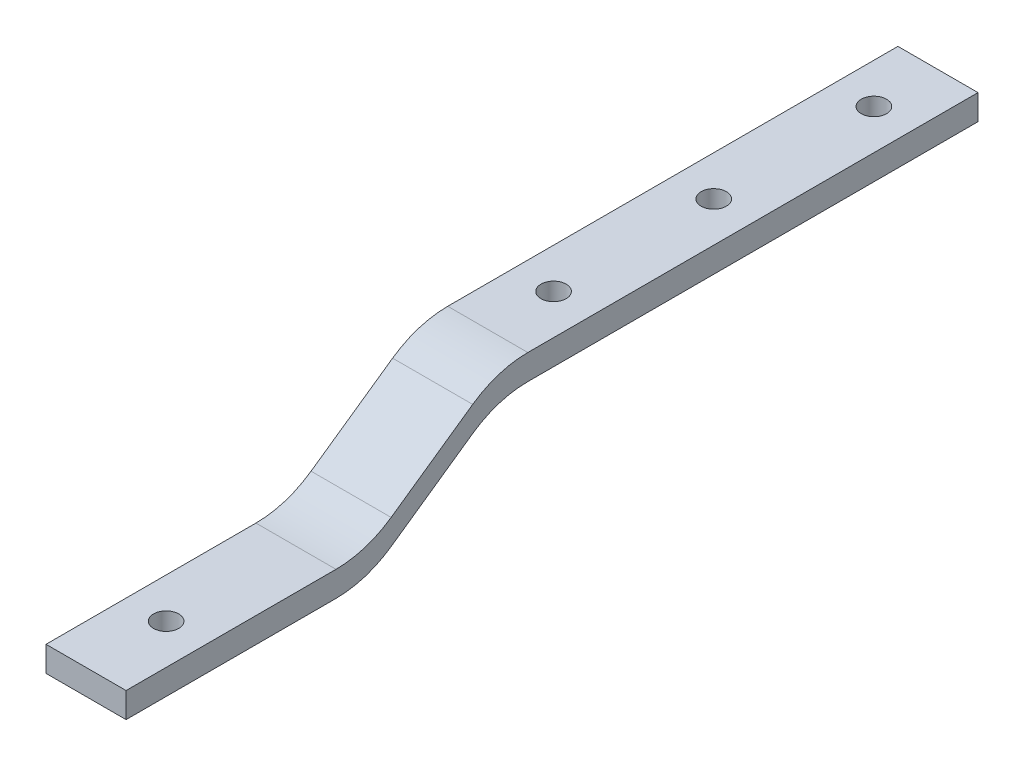
SolidWorks part; units mm, degrees
ref_plane "Front Plane" through (0, 0, 0) normal (0, 0, 1) x (1, 0, 0)
ref_plane "Top Plane" through (0, 0, 0) normal (0, 1, 0) x (1, 0, 0)
ref_plane "Right Plane" through (0, 0, 0) normal (1, 0, 0) x (0, 0, -1)
sketch "Sketch1" plane through (0, 0, 0) normal (1, 0, 0) x (0, 0, -1)
  line L0 (0, 2) -> (19.05, 2)
  line L1 (19.05, 2) -> (29.4532, 9.2844)
  line L2 (67.5532, 9.2844) -> (29.4532, 9.2844)
  line L3 (67.5532, 7.2844) -> (67.5532, 9.2844)
  line L4 (67.5532, 7.2844) -> (29.4532, 7.2844)
  line L5 (29.4532, 7.2844) -> (19.05, 0)
  line L6 (19.05, 0) -> (0, 0)
  line L7 (0, 0) -> (0, 2)
  dimension "D1" = 2
  dimension "D2" = 2
  dimension "D3" = 19.05
  dimension "D4" = 38.1
  dimension "D5" = 145
  dimension "D6" = 12.7
extrude "Boss-Extrude1" add sketch "Sketch1" along normal blind 6.35
sketch "Sketch2" plane through (0, 2, 0) normal (0, 1, 0) x (1, 0, 0)
  line L0 (6.35, 19.05) -> (6.35, 0) construction
  line L1 (6.35, 0) -> (0, 0) construction
  circle A0 centre (3.175, 6.35) radius 1
  dimension "D1" = 2
  dimension "D2" = 3.175
  dimension "D3" = 6.35
extrude "Cut-Extrude1" cut sketch "Sketch2" against normal up to surface (2 mm away) up to face at (3.175, 0, -9.525)
sketch "Sketch3" plane through (0, 9.2844, 0) normal (0, 1, 0) x (1, 0, 0)
  line L0 (6.35, 67.5532) -> (0, 67.5532) construction
  line L1 (6.35, 67.5532) -> (6.35, 29.4532) construction
  circle A0 centre (3.175, 62.4732) radius 1
  dimension "D1" = 2
  dimension "D2" = 5.08
  dimension "D3" = 3.175
extrude "Cut-Extrude2" cut sketch "Sketch3" against normal up to surface (2 mm away) up to face at (3.175, 7.2844, -48.5032)
pattern_linear "LPattern1" count 3 spacing 12.7 along (0, 0, 1) of "Cut-Extrude2"
fillet "Fillet1" radius 7.62 4 edges at (3.175, 0, -19.05) (3.175, 7.2844, -29.4532) (3.175, 2, -19.05) (3.175, 9.2844, -29.4532)
